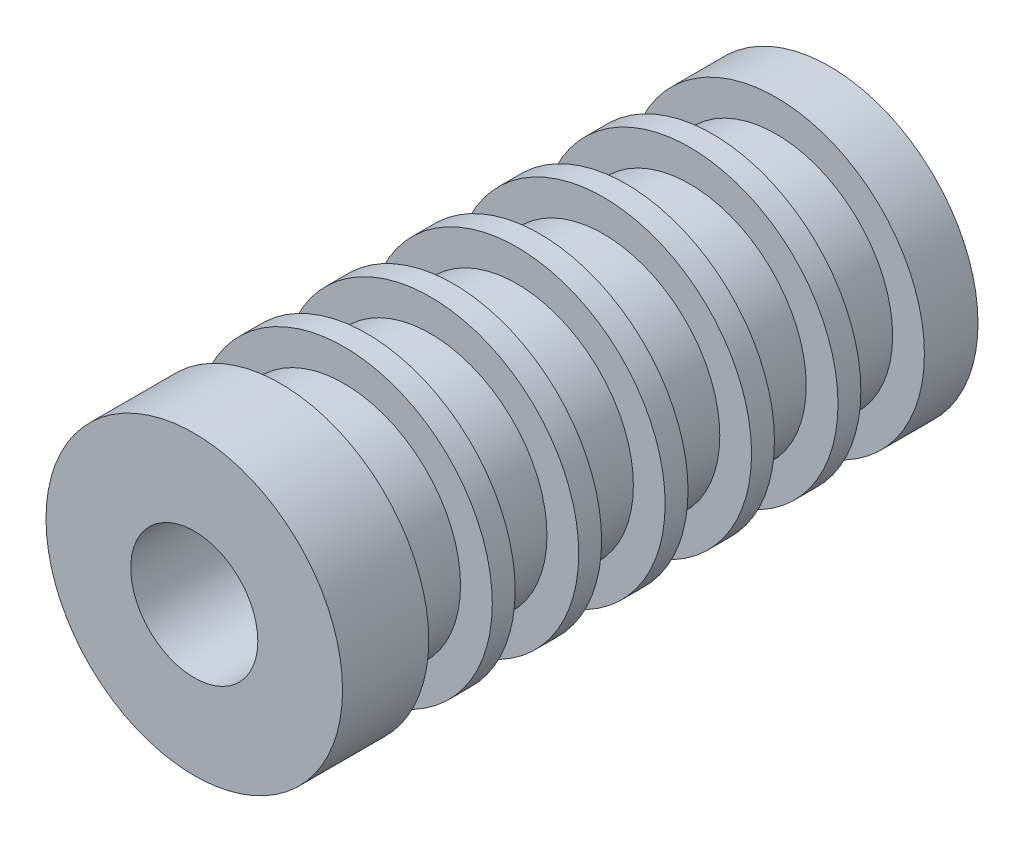
SolidWorks part; units mm, degrees
material "AISI 304"
ref_plane "Front Plane" through (0, 0, 0) normal (0, 0, 1) x (1, 0, 0)
ref_plane "Top Plane" through (0, 0, 0) normal (0, 1, 0) x (1, 0, 0)
ref_plane "Right Plane" through (0, 0, 0) normal (1, 0, 0) x (0, 0, -1)
sketch "Sketch1" plane through (0, 0, 0) normal (0, 0, 1) x (1, 0, 0)
  circle A0 centre (0, 0) radius 11.1125
  circle A1 centre (0, 0) radius 3.2004
  dimension "OD" = 22.225
  dimension "ID" = 6.4008
extrude "Extrude1" add sketch "Sketch1" along normal mid plane 50.8
sketch "Sketch2" plane through (0, 0, 0) normal (1, 0, 0) x (0, 0, -1)
  line L0 (-25.4, -3.2004) -> (25.4, -3.2004) construction
  line L3 (25.4, 3.2004) -> (-25.4, 3.2004) construction
  line L5 (-25.4, -3.2004) -> (25.4, -3.2004)
  line L6 (25.4, 3.2004) -> (-25.4, 3.2004)
sketch "Sketch4" plane through (0, 0, 25.4) normal (0, 0, 1) x (1, 0, 0)
  line L0 (0, 0) -> (-2.263, 2.263)
  line L1 (0, -12.2237) -> (0, 12.2237) construction
  circle A0 centre (0, 0) radius 3.2004 construction
  dimension "D1" = 45
sketch "Sketch5" plane through (0, 0, 25.4) normal (0, 0, 1) x (1, 0, 0)
  circle A0 centre (0, 0) radius 3.2004 construction
  circle A1 centre (0, 0) radius 11.1125
  circle A2 centre (0, 0) radius 11.1125
  circle A3 centre (0, 0) radius 3.2004
  dimension "D1" = 0
extrude "Cut-Extrude1" cut sketch "Sketch5" against normal blind 3.175
sketch "Sketch6" plane through (0, 0, 22.225) normal (0, 0, 1) x (1, 0, 0)
  circle A0 centre (0, 0) radius 4.7625
  dimension "D1" = 9.525
extrude "Cut-Extrude2" cut sketch "Sketch6" against normal through all
sketch "Sketch7" plane through (0, 0, -25.4) normal (0, 0, -1) x (-1, 0, 0)
  circle A0 centre (0, 0) radius 8.7312
  circle A1 centre (0, 0) radius 11.1125 construction
  circle A2 centre (0, 0) radius 11.1125
  dimension "D1" = 17.4625
extrude "Cut-Extrude3" cut sketch "Sketch7" against normal blind 4.7625 from offset 4.0164 offset against normal yes
pattern_linear "LPattern1" count 6 spacing 6.477 along (0, 0, 1) of "Cut-Extrude3"
